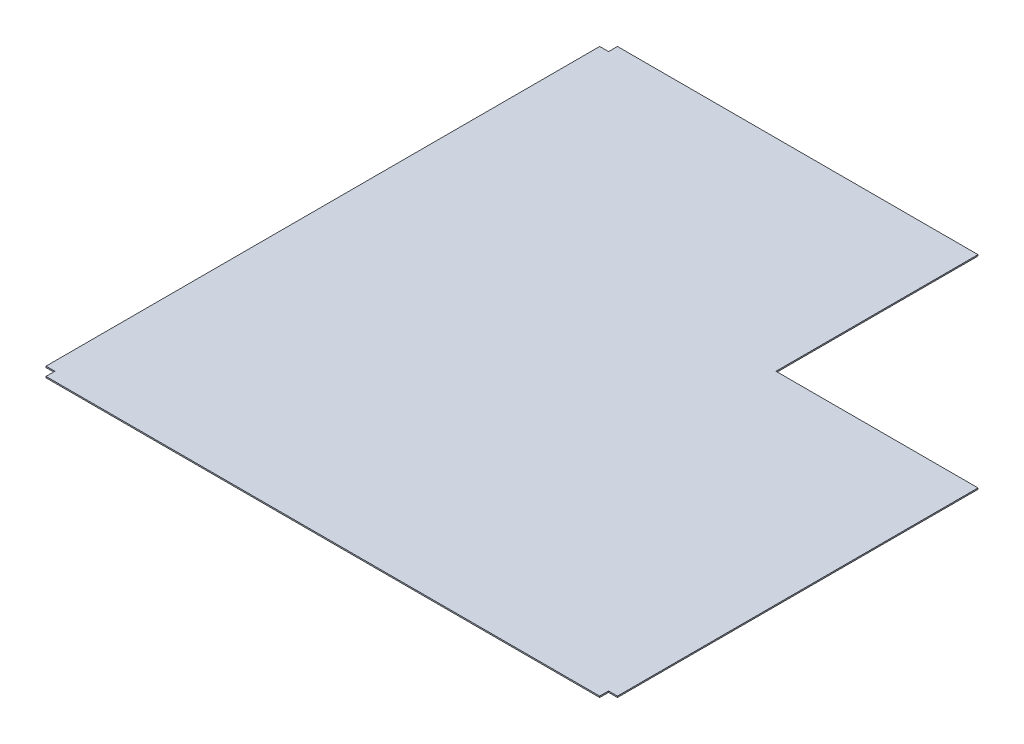
SolidWorks part; units mm, degrees
ref_plane "정면" through (0, 0, 0) normal (0, 0, 1) x (1, 0, 0)
ref_plane "윗면" through (0, 0, 0) normal (0, 1, 0) x (1, 0, 0)
ref_plane "우측면" through (0, 0, 0) normal (1, 0, 0) x (0, 0, -1)
sketch "스케치1" plane through (0, 0, 0) normal (0, 1, 0) x (1, 0, 0)
  line L0 (0, 0) -> (0, -6.9)
  line L1 (0, -6.9) -> (-6.9, -6.9)
  line L2 (-6.9, -6.9) -> (-6.9, -436.9)
  line L3 (-6.9, -436.9) -> (0, -436.9)
  line L4 (0, -436.9) -> (0, -443.8)
  line L5 (0, -443.8) -> (430, -443.8)
  line L6 (430, -443.8) -> (430, -436.9)
  line L7 (430, -436.9) -> (436.9, -436.9)
  line L8 (436.9, -436.9) -> (436.9, -156.9)
  line L9 (436.9, -156.9) -> (280, -156.9)
  line L10 (280, -156.9) -> (280, 0)
  line L11 (280, 0) -> (0, 0)
  dimension "D1" = 6.9
  dimension "D2" = 6.9
  dimension "D3" = 430
  dimension "D4" = 6.9
  dimension "D5" = 430
  dimension "D6" = 6.9
  dimension "D7" = 6.9
  dimension "D8" = 280
  dimension "D9" = 280
extrude "보스-돌출1" add sketch "스케치1" along normal blind 1
